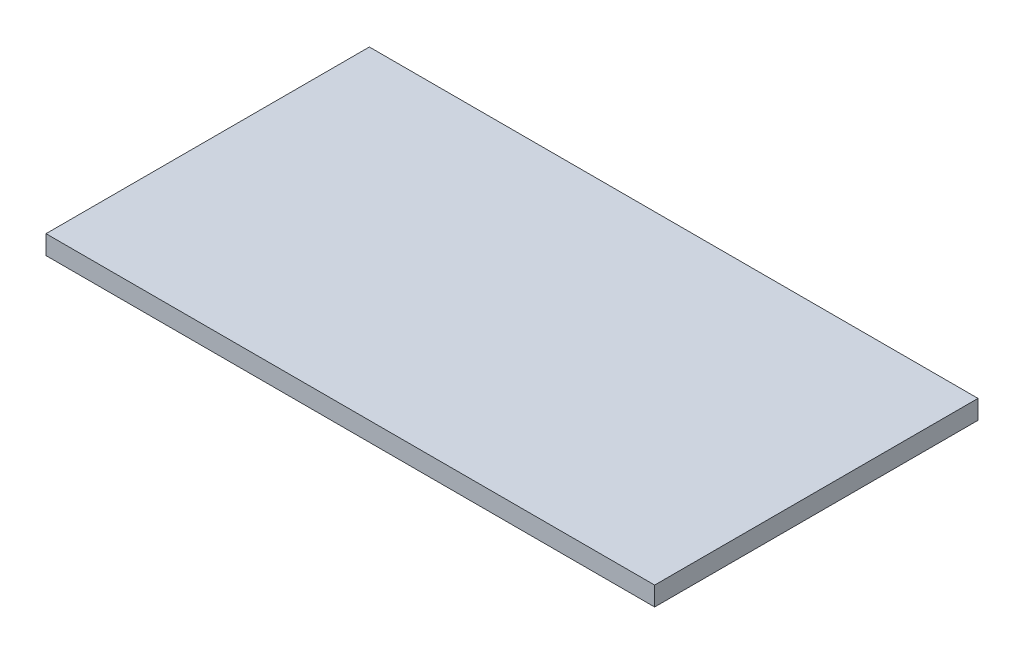
SolidWorks part; units mm, degrees
ref_plane "Front Plane" through (0, 0, 0) normal (0, 0, 1) x (1, 0, 0)
ref_plane "Top Plane" through (0, 0, 0) normal (0, 1, 0) x (1, 0, 0)
ref_plane "Right Plane" through (0, 0, 0) normal (1, 0, 0) x (0, 0, -1)
sketch "Sketch1" plane through (0, 0, 0) normal (0, 1, 0) x (1, 0, 0)
  line L1 (-50.8, -26.9875) -> (50.8, -26.9875)
  line L2 (-50.8, -26.9875) -> (-50.8, 26.9875)
  line L3 (-50.8, 26.9875) -> (50.8, 26.9875)
  line L4 (50.8, -26.9875) -> (50.8, 26.9875)
  line L5 (-50.8, -26.9875) -> (50.8, 26.9875) construction
  line L6 (-50.8, 26.9875) -> (50.8, -26.9875) construction
  point P0 (0, 0)
  dimension "D1" = 53.975
  dimension "D2" = 101.6
extrude "Boss-Extrude1" add sketch "Sketch1" along normal blind 3.175
